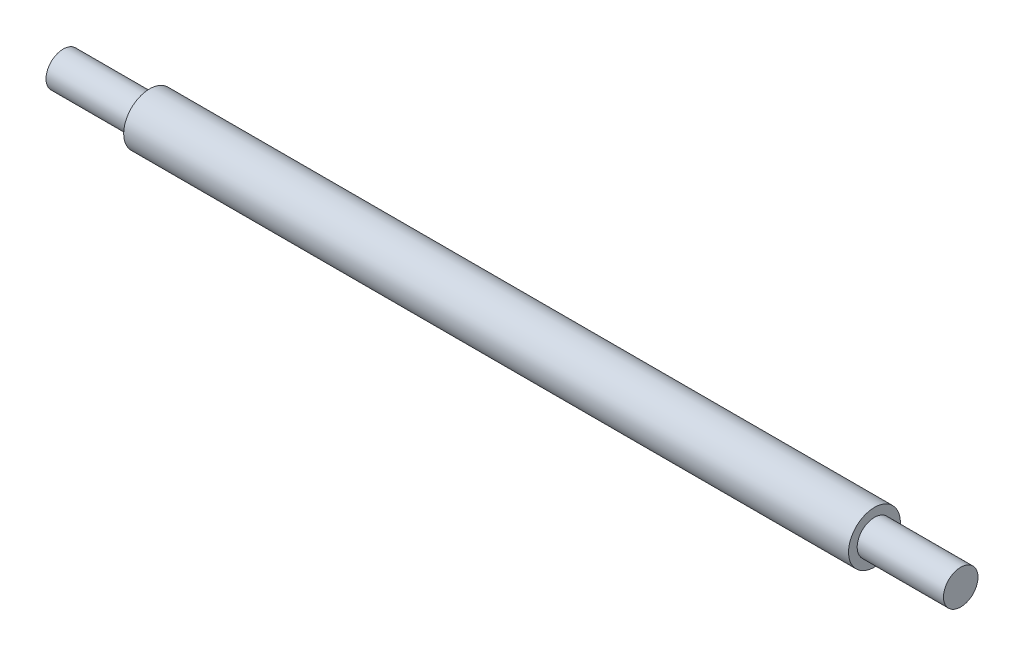
SolidWorks part; units mm, degrees
ref_plane "Ön Düzlem" through (0, 0, 0) normal (0, 0, 1) x (1, 0, 0)
ref_plane "Üst Düzlem" through (0, 0, 0) normal (0, 1, 0) x (1, 0, 0)
ref_plane "Sağ Düzlem" through (0, 0, 0) normal (1, 0, 0) x (0, 0, -1)
sketch "Çizim1" plane through (0, 0, 0) normal (1, 0, 0) x (0, 0, -1)
  circle A0 centre (0, 0) radius 2
  dimension "D1" = 4
extrude "Yükseklik-Ekstrüzyon1" add sketch "Çizim1" against normal blind 10
sketch "Çizim2" plane through (-10, 0, 0) normal (-1, 0, 0) x (0, 0, 1)
  circle A0 centre (0, 0) radius 3
  dimension "D1" = 6
extrude "Yükseklik-Ekstrüzyon2" add sketch "Çizim2" along normal blind 84
sketch "Çizim3" plane through (-94, 0, 0) normal (-1, 0, 0) x (0, 0, 1)
  circle A0 centre (0, 0) radius 2
  dimension "D1" = 4
extrude "Yükseklik-Ekstrüzyon3" add sketch "Çizim3" along normal blind 10
